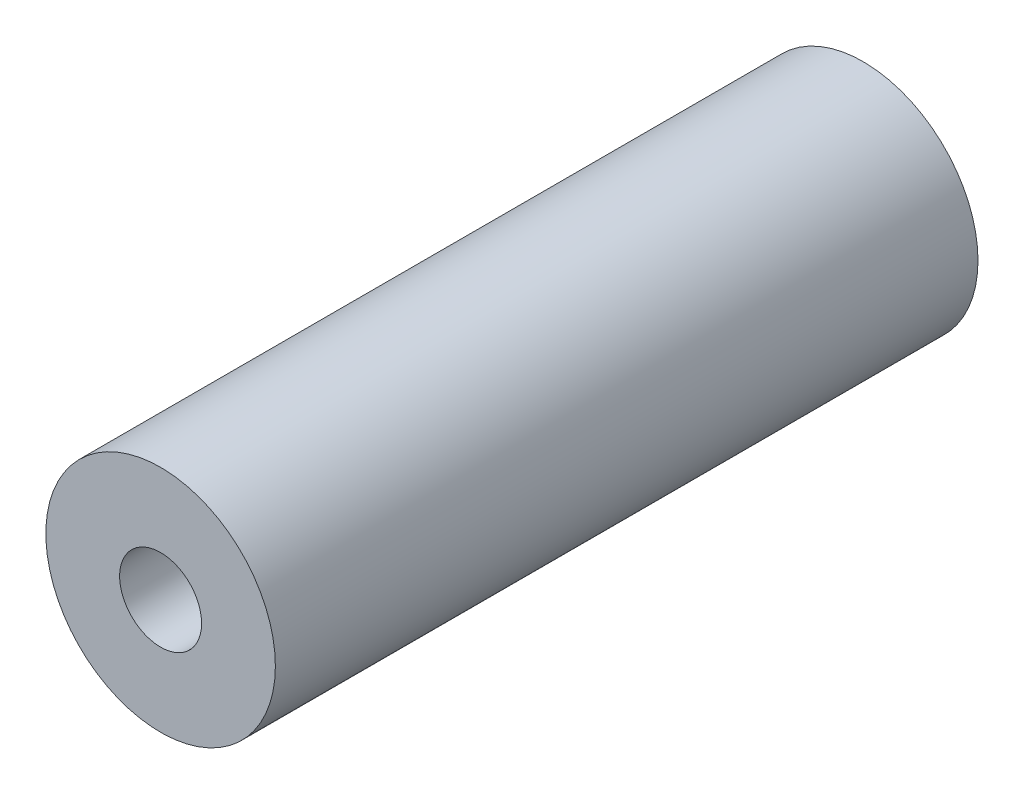
SolidWorks part; units mm, degrees
ref_plane "Front Plane" through (0, 0, 0) normal (0, 0, 1) x (1, 0, 0)
ref_plane "Top Plane" through (0, 0, 0) normal (0, 1, 0) x (1, 0, 0)
ref_plane "Right Plane" through (0, 0, 0) normal (1, 0, 0) x (0, 0, -1)
sketch "Sketch1" plane through (0, 0, 0) normal (0, 0, 1) x (1, 0, 0)
  circle A0 centre (0, 0) radius 4.9
  circle A1 centre (0, 0) radius 1.75
extrude "Boss-Extrude1" add sketch "Sketch1" along normal blind 30
